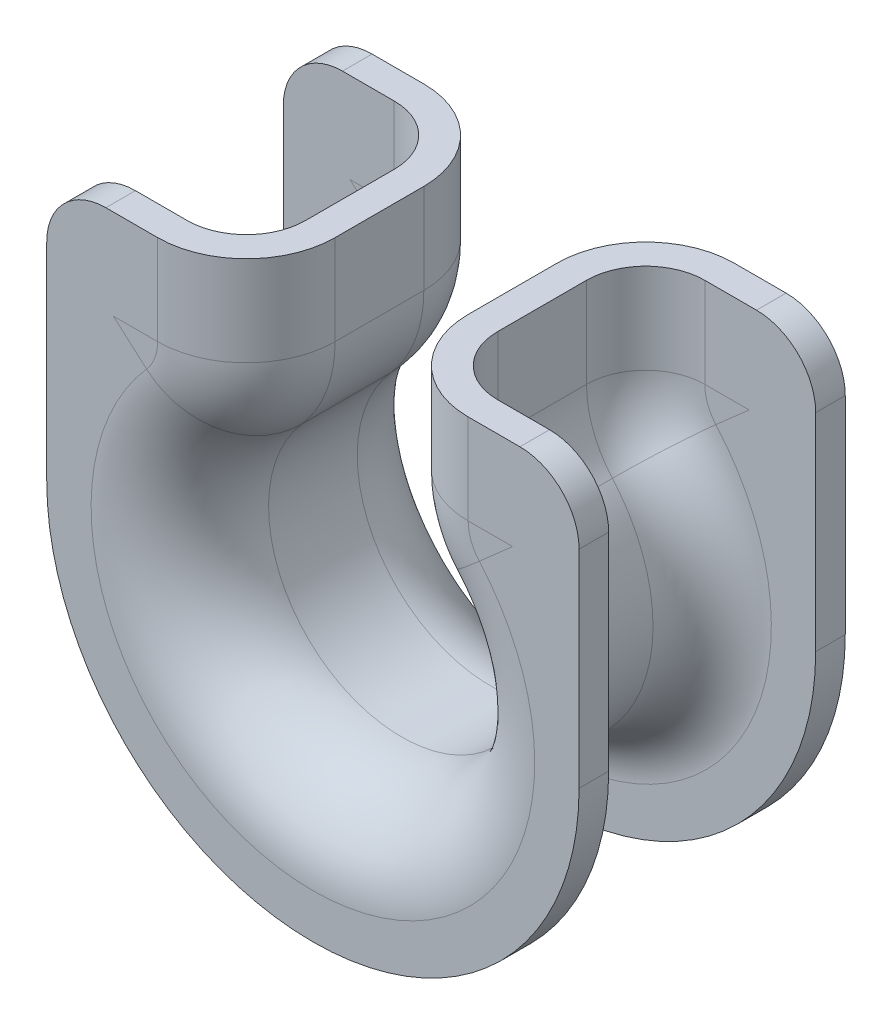
SolidWorks part; units mm, degrees
ref_plane "Front Plane" through (0, 0, 0) normal (0, 0, 1) x (1, 0, 0)
ref_plane "Top Plane" through (0, 0, 0) normal (0, 1, 0) x (1, 0, 0)
ref_plane "Right Plane" through (0, 0, 0) normal (1, 0, 0) x (0, 0, -1)
sketch "Sketch1" plane through (0, 0, 0) normal (0, 0, 1) x (1, 0, 0)
  line L0 (0, 0) -> (0, 18.5911) construction
  line L1 (4.5, 11.9059) -> (4.5, 18)
  line L2 (-4.5, 11.9059) -> (-4.5, 18)
  arc A0 (-6.75, 5.9529) -> (6.75, 5.9529) centre (0, 0) ccw
  arc A1 (4.5, 11.9059) -> (6.75, 5.9529) centre (13.5, 11.9059) ccw
  arc A2 (-4.5, 11.9059) -> (-6.75, 5.9529) centre (-13.5, 11.9059) cw
  point P1 (0, 0)
  point P9 (0, 0)
  dimension "D1" = 18
  dimension "D4" = 9
  dimension "D2" = 9
  dimension "D3" = 18
ref_plane "Plane1" through (-4.5, 18, 0) normal (0, 1, 0) x (1, 0, 0)
sketch "Sketch2" plane through (-4.5, 18, 0) normal (0, 1, 0) x (1, 0, 0)
  line L0 (-6, 3) -> (-6, -3) construction
  line L1 (-4.5, 0) -> (13.5, 0) construction
  line L2 (0, 3) -> (0, -3)
  line L4 (-6, 9) -> (1.4953, 9) construction
  line L5 (-6, -9) -> (1.6863, -9) construction
  line L6 (-2, 3) -> (-2, -3)
  line L8 (-6, 9) -> (-9, 9)
  line L9 (-9, 9) -> (-9, 7)
  line L10 (-9, 7) -> (-6, 7)
  line L11 (-6, 0) -> (-9.6923, 0) construction
  line L12 (-10, 3) -> (-10, -3) construction
  line L13 (-12, 3) -> (-12, -3) construction
  line L14 (-9, -7) -> (-6, -7)
  line L15 (-9, -9) -> (-9, -7)
  line L16 (-6, -9) -> (-9, -9)
  arc A0 (0, 3) -> (-6, 9) centre (-6, 3) ccw
  arc A2 (-6, -7) -> (-2, -3) centre (-6, -3) ccw
  arc A3 (-2, 3) -> (-6, 7) centre (-6, 3) ccw
  arc A4 (-6, -9) -> (0, -3) centre (-6, -3) ccw
  arc A5 (0, 3) -> (-12, 3) centre (-6, 3) ccw construction
  arc A6 (-2, 3) -> (-10, 3) centre (-6, 3) ccw construction
  arc A7 (-12, -3) -> (0, -3) centre (-6, -3) ccw construction
  arc A8 (-10, -3) -> (-2, -3) centre (-6, -3) ccw construction
  point P4 (-6, 0)
  point P29 (0, 0)
  point P30 (-6, -3)
  point P31 (-6, -3)
  dimension "D2" = 6
  dimension "D1" = 18
  dimension "D4" = 3
  dimension "D3" = 2
sweep "Sweep3" add profiles "Sketch2" path "Sketch1"
sketch "Sketch3" plane through (0, 0, 9) normal (0, 0, 1) x (1, 0, 0)
  line L0 (-18, 0) -> (-18, 18)
  line L1 (-18, 18) -> (-13.5, 18)
  line L3 (13.5, 11.9059) -> (11.25, 9.9216) construction
  line L6 (-13.5, 18) -> (-13.5, 11.9059) construction
  line L9 (13.5, 11.9059) -> (11.25, 9.9216)
  line L10 (0, 0) -> (0, 4.6722) construction
  line L11 (13.5, 18) -> (13.5, 11.9059)
  line L12 (-13.5, 18) -> (-13.5, 11.9059)
  line L13 (18, 18) -> (13.5, 18)
  line L14 (18, 0) -> (18, 18)
  arc A0 (-13.5, 11.9059) -> (13.5, 11.9059) centre (0, 0) ccw construction
  arc A2 (-13.5, 11.9059) -> (13.5, 11.9059) centre (0, 0) ccw construction
  arc A4 (-13.5, 11.9059) -> (-18, 0) centre (0, 0) ccw
  arc A5 (13.5, 11.9059) -> (18, 0) centre (0, 0) cw
  line M4 (-13.5, 18) -> (-13.5, 11.9059)
extrude "Boss-Extrude1" add sketch "Sketch3" against normal blind 2 contours A4 L1 L0 M4 | L11 A5 L14 L13
mirror "Mirror2" about plane through (0, 0, 0) normal (0, 0, 1) of "Boss-Extrude1"
fillet "Fillet1" radius 4 4 edges at (-18, 18, -8) (-18, 18, 8) (18, 18, 8) (18, 18, -8)
